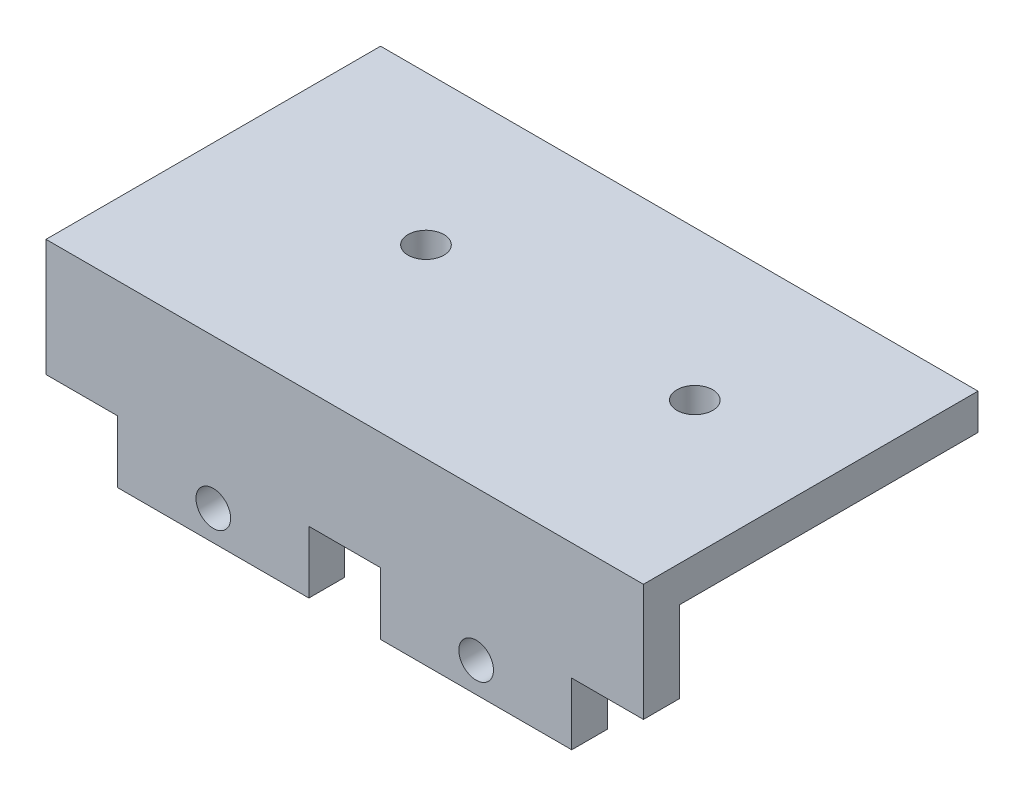
SolidWorks part; units mm, degrees
ref_plane "Front Plane" through (0, 0, 0) normal (0, 0, 1) x (1, 0, 0)
ref_plane "Top Plane" through (0, 0, 0) normal (0, 1, 0) x (1, 0, 0)
ref_plane "Right Plane" through (0, 0, 0) normal (1, 0, 0) x (0, 0, -1)
sketch "Sketch1" plane through (0, 0, 0) normal (0, 1, 0) x (1, 0, 0)
  line L0 (-11.25, 0) -> (11.25, 0)
  line L1 (-25, -12.5) -> (25, -12.5)
  line L2 (-25, -12.5) -> (-25, 12.5)
  line L3 (-25, 12.5) -> (25, 12.5)
  line L4 (25, -12.5) -> (25, 12.5)
  line L5 (-25, -12.5) -> (25, 12.5) construction
  line L6 (-25, 12.5) -> (25, -12.5) construction
  circle A0 centre (-11.25, 0) radius 1.3
  circle A1 centre (11.25, 0) radius 4.5
  point P0 (0, 0)
  point P10 (0, 0)
  dimension "D3" = 2.6
  dimension "D4" = 9
  dimension "D1" = 25
  dimension "D2" = 50
  dimension "D5" = 22.5
extrude "Boss-Extrude1" add sketch "Sketch1" along normal mid plane 5
sketch "Sketch2" plane through (0, 0, 12.5) normal (0, 0, 1) x (1, 0, 0)
  line L0 (-25, 2.5) -> (-25, -2.5) construction
  line L1 (-25, -2.5) -> (25, -2.5)
  line L2 (-25, -2.5) -> (-25, 9.5)
  line L3 (-25, 9.5) -> (25, 9.5)
  line L4 (25, -2.5) -> (25, 9.5)
  line L5 (-25, -2.5) -> (25, -2.5) construction
  dimension "D1" = 50
  dimension "D2" = 12
extrude "Boss-Extrude2" add sketch "Sketch2" along normal blind 3
sketch "Sketch3" plane through (0, 9.5, 0) normal (0, 1, 0) x (1, 0, 0)
  line L0 (-25, -15.5) -> (-25, -12.5) construction
  line L1 (-25, -15.5) -> (25, -15.5)
  line L2 (-25, -15.5) -> (-25, 12.5)
  line L3 (-25, 12.5) -> (25, 12.5)
  line L4 (25, -15.5) -> (25, 12.5)
  line L5 (-25, 12.5) -> (25, 12.5) construction
extrude "Boss-Extrude3" add sketch "Sketch3" along normal blind 3
sketch "Sketch4" plane through (0, 12.5, 0) normal (0, 1, 0) x (1, 0, 0)
  line L0 (11.25, 0) -> (-11.25, 0)
  line L1 (-25, 12.5) -> (25, 12.5) construction
  line L2 (-25, -15.5) -> (-25, 12.5) construction
  circle A0 centre (11.25, 0) radius 1.3
  circle A1 centre (-11.25, 0) radius 1.3
  dimension "D1" = 2.6
  dimension "D2" = 2.6
  dimension "D3" = 11.25
  dimension "D4" = 12.5
  dimension "D5" = 13.75
extrude "Cut-Extrude1" cut sketch "Sketch4" against normal through all
sketch "Sketch5" plane through (0, -2.5, 0) normal (0, -1, 0) x (1, 0, 0)
  line L11 (21.45, -10.3) -> (21.45, 10.2) construction
  line L20 (0.95, 10.2) -> (41.95, 10.2) construction
  line L21 (0.95, 10.2) -> (0.95, -10.3) construction
  line L22 (0.95, -10.3) -> (41.95, -10.3) construction
  line L23 (41.95, 10.2) -> (41.95, -10.3) construction
  line L24 (-5.05, 16.2) -> (47.95, 16.2)
  line L25 (47.95, 16.2) -> (47.95, -16.3)
  line L26 (-5.05, -16.3) -> (47.95, -16.3)
  line L27 (-5.05, 16.2) -> (-5.05, -16.3)
  line L28 (0.45, 10.7) -> (42.45, 10.7)
  line L29 (42.45, 10.7) -> (42.45, -10.8)
  line L30 (0.45, -10.8) -> (42.45, -10.8)
  line L31 (0.45, 10.7) -> (0.45, -10.8)
  circle A5 centre (11.25, 0) radius 7.5 construction
  circle A6 centre (45.75, -5) radius 1.6
  circle A7 centre (45.75, 4.9) radius 1.6
  circle A8 centre (-2.85, 4.9) radius 1.6
  circle A9 centre (-2.85, -5) radius 1.6
  dimension "D4" = 10.3
  dimension "D5" = 10.3
  dimension "D8" = 3.8
  dimension "D9" = 5.3
  dimension "D1" = 15
  dimension "D6" = 3.2
  dimension "D7" = 3.2
  dimension "D2" = 41
  dimension "D3" = 20.5
  dimension "D10" = 5.3
  dimension "D11" = 6
  dimension "D12" = 0.5
extrude "Boss-Extrude4" add sketch "Sketch5" along normal blind 4
sketch "Sketch7" plane through (0, -2.5, 0) normal (0, -1, 0) x (1, 0, 0)
  circle A0 centre (11.25, 0) radius 8
  dimension "D1" = 16
extrude "Cut-Extrude2" cut sketch "Sketch7" against normal up to surface (5 mm away) up to face at (11.25, 2.5, 4.5)
sketch "Sketch8" plane through (0, -2.5, 0) normal (0, -1, 0) x (1, 0, 0)
  line L4 (0.45, 10.7) -> (0.45, -10.8)
  line L5 (0.45, 10.7) -> (0.45, -10.8)
  line L6 (0.45, -10.8) -> (25, -10.8)
  line L7 (25, -10.8) -> (25, 10.7)
  line L11 (25, -10.8) -> (25, 10.7)
  line L12 (0.45, -10.8) -> (25, -10.8)
  line L13 (25, 10.7) -> (0.45, 10.7)
  line L14 (25, 10.7) -> (0.45, 10.7)
  dimension "D1" = 0
extrude "Cut-Extrude3" cut sketch "Sketch8" against normal blind 3.8
sketch "Sketch9" plane through (25, 0, 0) normal (1, 0, 0) x (0, 0, -1)
  line L0 (-12.5, 2.5) -> (-15.5, 2.5)
  line L1 (-15.5, 2.5) -> (-16.2, 2.5)
  line L2 (-16.2, 2.5) -> (-16.2, -2.5)
  line L3 (-16.2, -2.5) -> (-15.5, -2.5)
  line L12 (-10.7, 1.3) -> (10.8, 1.3)
  line L13 (-10.7, -2.5) -> (-10.7, 1.3)
  line L14 (10.8, -2.5) -> (12.5, -2.5)
  line L15 (12.5, -2.5) -> (12.5, 2.5)
  line L16 (12.5, 2.5) -> (-12.5, 2.5)
  line L17 (-12.5, 2.5) -> (-12.5, 9.5)
  line L18 (-12.5, 9.5) -> (12.5, 9.5)
  line L19 (12.5, 9.5) -> (12.5, 12.5)
  line L20 (12.5, 12.5) -> (-15.5, 12.5)
  line L21 (-15.5, 12.5) -> (-15.5, -2.5)
  line L22 (-15.5, -2.5) -> (-10.7, -2.5)
  line L23 (-10.7, -2.5) -> (-10.7, 1.3)
  line L24 (-10.7, 1.3) -> (10.8, 1.3)
  line L26 (10.8, -2.5) -> (12.5, -2.5)
  line L27 (12.5, -2.5) -> (12.5, 2.5)
  line L28 (12.5, 2.5) -> (-12.5, 2.5)
  line L29 (-12.5, 2.5) -> (-12.5, 9.5)
  line L30 (-12.5, 9.5) -> (12.5, 9.5)
  line L31 (12.5, 9.5) -> (12.5, 12.5)
  line L32 (12.5, 12.5) -> (-15.5, 12.5)
  line L33 (-15.5, 12.5) -> (-15.5, -2.5)
  line L34 (-15.5, -2.5) -> (-10.7, -2.5)
  line L40 (10.8, 1.3) -> (10.8, -2.5)
  line L41 (10.8, 1.3) -> (10.8, -2.5)
  dimension "D1" = 0
extrude "Boss-Extrude6" add sketch "Sketch9" along normal up to surface (22.95 mm away) up to face at (47.95, -4.5, -0.05)
sketch "Sketch10" plane through (47.95, 0, 0) normal (1, 0, 0) x (0, 0, -1)
  line L6 (16.3, -2.5) -> (12.5, -2.5)
  line L7 (12.5, -2.5) -> (12.5, 2.5)
  line L8 (12.5, 2.5) -> (-16.2, 2.5)
  line L9 (-16.2, 2.5) -> (-16.2, -6.5)
  line L10 (-16.2, -6.5) -> (16.3, -6.5)
  line L11 (16.3, -6.5) -> (16.3, -2.5)
  line L12 (16.3, -2.5) -> (12.5, -2.5)
  line L13 (12.5, -2.5) -> (12.5, 2.5)
  line L14 (12.5, 2.5) -> (-16.2, 2.5)
  line L15 (-16.2, 2.5) -> (-16.2, -6.5)
  line L16 (-16.2, -6.5) -> (16.3, -6.5)
  line L17 (16.3, -6.5) -> (16.3, -2.5)
  dimension "D1" = 0
extrude "Boss-Extrude7" add sketch "Sketch10" along normal blind 2
sketch "Sketch11" plane through (0, 1.3, 0) normal (0, -1, 0) x (1, 0, 0)
  circle A0 centre (-2.85, 4.9) radius 1.6 construction
  circle A1 centre (-2.85, -5) radius 1.6 construction
  circle A2 centre (45.75, 4.9) radius 1.6 construction
  circle A3 centre (45.75, -5) radius 1.6 construction
  circle A4 centre (-2.85, 4.9) radius 1.6
  circle A5 centre (-2.85, -5) radius 1.6
  circle A6 centre (45.75, 4.9) radius 1.6
  circle A7 centre (45.75, -5) radius 1.6
extrude "Cut-Extrude4" cut sketch "Sketch11" against normal up to surface (1.2 mm away) up to face at (11.25, 2.5, 8)
sketch "Sketch12" plane through (0, 1.3, 0) normal (0, -1, 0) x (1, 0, 0)
  line L0 (49.95, 16.2) -> (49.95, -16.3) construction
  line L1 (42.95, 10.7) -> (49.95, 10.7)
  line L2 (42.95, 10.7) -> (42.95, -10.3)
  line L3 (42.95, -10.3) -> (49.95, -10.3)
  line L4 (49.95, 10.7) -> (49.95, -10.3)
  line L6 (0.45, 10.7) -> (0.45, -10.8) construction
  line L7 (47.95, 10.7) -> (0.45, 10.7) construction
  line L8 (0.45, 10.7) -> (42.45, 10.7) construction
  circle A0 centre (45.75, 4.9) radius 1.6 construction
  circle A1 centre (45.75, -5) radius 1.6 construction
  circle A2 centre (45.75, 4.9) radius 1.6
  circle A3 centre (45.75, -5) radius 1.6
  dimension "D1" = 42.5
  dimension "D2" = 21
extrude "Boss-Extrude8" add sketch "Sketch12" along normal up to surface (7.8 mm away) up to face at (22.45, -6.5, -0.05)
sketch "Sketch13" plane through (25, 0, 0) normal (-1, 0, 0) x (0, 0, 1)
  line L1 (15.5, 2.5) -> (16.2, 2.5)
  line L2 (15.5, 2.5) -> (15.5, -6.5)
  line L3 (15.5, -6.5) -> (16.2, -6.5)
  line L4 (16.2, 2.5) -> (15.5, 2.5)
  line L5 (15.5, 2.5) -> (15.5, -2.5)
  line L6 (15.5, -2.5) -> (16.2, -2.5)
  line L7 (16.2, -2.5) -> (16.2, 2.5)
  line L8 (16.2, 2.5) -> (15.5, 2.5)
  line L9 (15.5, 2.5) -> (15.5, -2.5)
  line L11 (16.2, -2.5) -> (16.2, 2.5)
  line L12 (16.2, 2.5) -> (16.2, -6.5)
  line M5 (16.2, 2.5) -> (15.5, 2.5)
  line M6 (15.5, 2.5) -> (15.5, -2.5)
  line M7 (15.5, -2.5) -> (16.2, -2.5)
  line M8 (16.2, -2.5) -> (16.2, 2.5)
  dimension "D1" = 0
extrude "Cut-Extrude5" cut sketch "Sketch13" against normal through all both and the other way through all contours M8 M5 M6 M7 | L12 L2 L3 M7
sketch "Sketch14" plane through (-25, 0, 0) normal (-1, 0, 0) x (0, 0, 1)
  line L1 (-16.3, -6.5) -> (12.5, -6.5)
  line L2 (-16.3, -6.5) -> (-16.3, 2.5)
  line L3 (-16.3, 2.5) -> (12.5, 2.5)
  line L4 (12.5, -6.5) -> (12.5, 2.5)
  line L5 (12.5, -6.5) -> (15.5, -6.5)
  line L6 (12.5, -6.5) -> (12.5, -2.5)
  line L7 (12.5, -2.5) -> (15.5, -2.5)
  line L8 (15.5, -6.5) -> (15.5, -2.5)
  line M5 (-12.5, -2.5) -> (15.5, -2.5)
  line M11 (12.5, 2.5) -> (-12.5, 2.5)
  line M12 (-12.5, 2.5) -> (-12.5, -2.5)
extrude "Cut-Extrude6" cut sketch "Sketch14" against normal through all both and the other way through all contours L5 L8 L4 M5 | L1 L4 L3 L2 M5 M12 | L4 M5 M11 M12
sketch "Sketch15" plane through (0, 2.5, 0) normal (0, 1, 0) x (1, 0, 0)
  line L4 (49.95, -12.5) -> (25, -12.5)
  line L5 (25, -12.5) -> (25, -15.5)
  line L6 (25, -15.5) -> (49.95, -15.5)
  line L7 (49.95, -15.5) -> (49.95, -12.5)
  line L8 (49.95, -12.5) -> (25, -12.5)
  line L9 (25, -12.5) -> (25, -15.5)
  line L10 (25, -15.5) -> (49.95, -15.5)
  line L11 (49.95, -15.5) -> (49.95, -12.5)
  dimension "D1" = 0
extrude "Cut-Extrude7" cut sketch "Sketch15" against normal through all both and the other way through all
sketch "Sketch16" plane through (0, 0, 15.5) normal (0, 0, 1) x (1, 0, 0)
  line L0 (-25, -2.5) -> (25, -2.5) construction
  line L1 (-25, -2.5) -> (-19, -2.5)
  line L2 (-25, -2.5) -> (-25, 2.7)
  line L3 (-25, 2.7) -> (-19, 2.7)
  line L4 (-19, -2.5) -> (-19, 2.7)
  line L5 (-3, -2.5) -> (3, -2.5)
  line L6 (-3, -2.5) -> (-3, 2.7)
  line L7 (-3, 2.7) -> (3, 2.7)
  line L8 (3, -2.5) -> (3, 2.7)
  line L14 (25, -2.5) -> (19, -2.5)
  line L15 (25, -2.5) -> (25, 2.7)
  line L16 (25, 2.7) -> (19, 2.7)
  line L17 (19, -2.5) -> (19, 2.7)
  circle A0 centre (-11, 0) radius 1.45
  circle A1 centre (11, 0) radius 1.45
  point P11 (0, 2.7)
  dimension "D8" = 2.9
  dimension "D9" = 2.9
  dimension "D1" = 11
  dimension "D2" = 11
  dimension "D3" = 2.5
  dimension "D4" = 6
  dimension "D5" = 6
  dimension "D6" = 6
  dimension "D7" = 5.2
extrude "Cut-Extrude8" cut sketch "Sketch16" against normal through all both and the other way through all
sketch "Sketch18" plane through (0, 12.5, 0) normal (0, 1, 0) x (1, 0, 0)
  circle A0 centre (-8.7, 0) radius 1.5
  dimension "D1" = 3
extrude "Cut-Extrude9" cut sketch "Sketch18" against normal through all both and the other way through all
sketch "Sketch19" plane through (0, 12.5, 0) normal (0, 1, 0) x (1, 0, 0)
  arc A0 (-10.0848, 0.5765) -> (-10.0848, -0.5765) centre (-11.25, 0) ccw construction
  arc A1 (-10.0848, 0.5765) -> (-10.0848, -0.5765) centre (-11.25, 0) ccw
  circle A2 centre (11.25, 0) radius 1.3 construction
  circle A3 centre (11.25, 0) radius 1.3
  circle A4 centre (-8.7, 0) radius 1.5
  circle M1 centre (11.25, 0) radius 1.3
  arc M2 (-10.0848, -0.5765) -> (-10.0848, 0.5765) centre (-11.25, 0) cw
extrude "Boss-Extrude9" add sketch "Sketch19" along direction (0, -1, 0) on the side against the normal blind 3 contours A4 M2 | M1
sketch "Sketch20" plane through (0, 12.5, 0) normal (0, 1, 0) x (1, 0, 0)
  circle A0 centre (13.8, 0) radius 1.5
  circle A1 centre (-8.7, 0) radius 1.5 construction
  dimension "D1" = 3
  dimension "D2" = 22.5
extrude "Cut-Extrude10" cut sketch "Sketch20" against normal through all both and the other way through all
